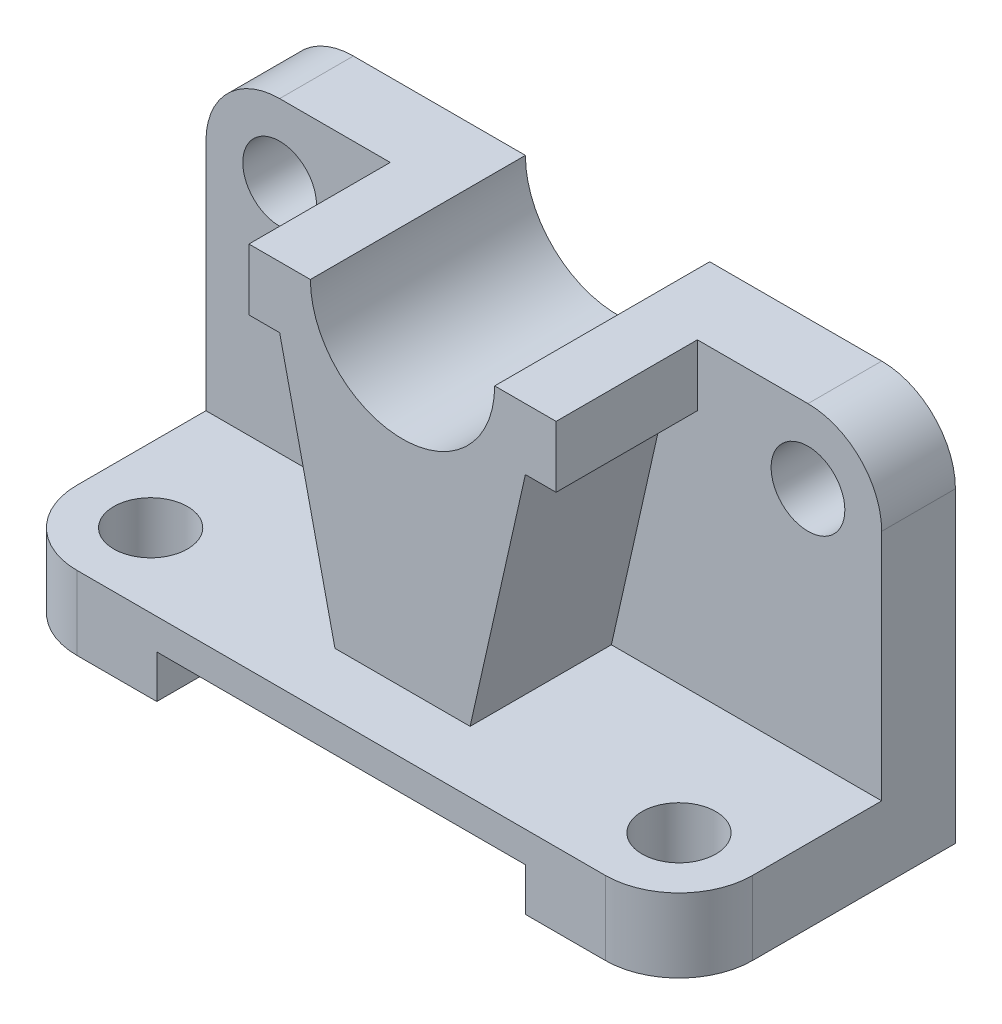
SolidWorks part; units mm, degrees
ref_plane "Front Plane" through (0, 0, 0) normal (0, 0, 1) x (1, 0, 0)
ref_plane "Top Plane" through (0, 0, 0) normal (0, 1, 0) x (1, 0, 0)
ref_plane "Right Plane" through (0, 0, 0) normal (1, 0, 0) x (0, 0, -1)
sketch "Sketch1" plane through (0, 0, 0) normal (1, 0, 0) x (0, 0, -1)
  line L0 (10.4243, 39.1655) -> (22.4243, 39.1655)
  line L1 (22.4243, 39.1655) -> (22.4243, -22.8345)
  line L2 (22.4243, -22.8345) -> (-22.5757, -22.8345)
  line L3 (-22.5757, -22.8345) -> (-22.5757, -10.8345)
  line L4 (-22.5757, -10.8345) -> (10.4243, -10.8345)
  line L5 (10.4243, 39.1655) -> (10.4243, -10.8345)
extrude "Boss-Extrude1" add sketch "Sketch1" along normal blind 110
fillet "Fillet1" radius 12 4 edges at (0, 39.1655, -16.4243) (0, -16.8345, 22.5757) (110, -16.8345, 22.5757) (110, 39.1655, -16.4243)
sketch "Sketch2" plane through (0, -10.8345, 0) normal (0, 1, 0) x (1, 0, 0)
  circle A0 centre (12, -10.5757) radius 6
  circle A1 centre (98, -10.5757) radius 6
extrude "Cut-Extrude1" cut sketch "Sketch2" against normal blind 12 contours A1 | A0
sketch "Sketch3" plane through (0, 0, -10.4243) normal (0, 0, 1) x (1, 0, 0)
  circle A0 centre (12, 27.1655) radius 6
  circle A1 centre (98, 27.1655) radius 6
extrude "Cut-Extrude3" cut sketch "Sketch3" against normal blind 12 contours A0 | A1
sketch "Sketch4" plane through (0, 0, 22.5757) normal (0, 0, 1) x (1, 0, 0)
  line L0 (25, -22.8345) -> (25, -15.8345)
  line L1 (98, -22.8345) -> (12, -22.8345) construction
  line L7 (25, -22.8345) -> (85, -22.8345)
  line L8 (25, -15.8345) -> (85, -15.8345)
  line L9 (85, -15.8345) -> (85, -22.8345)
extrude "Cut-Extrude4" cut sketch "Sketch4" against normal blind 60
sketch3d "3DSketch1"
  line L3 (30, 39.1655, -22.4243) -> (40, 39.1655, -22.4243)
  line L5 (70, 39.1655, -22.4243) -> (80, 39.1655, -22.4243)
  line L6 (30, 39.1655, -22.4243) -> (30, 29.1655, -22.4243)
  line L7 (30, 29.1655, -22.4243) -> (35, 29.1655, -22.4243)
  line L8 (80, 39.1655, -22.4243) -> (80, 29.1655, -22.4243)
  line L9 (80, 29.1655, -22.4243) -> (75, 29.1655, -22.4243)
  line L10 (35, 29.1655, -22.4243) -> (44, -10.8327, -22.4243)
  line L11 (55, -10.8327, -22.4243) -> (44, -10.8327, -22.4243) construction
  line L12 (44, -10.8327, -22.4243) -> (66, -10.8327, -22.4243)
  line L13 (75, 29.1655, -22.4243) -> (66, -10.8327, -22.4243)
  arc A0 (40, 39.1655, -22.4243) -> (70, 39.1655, -22.4243) centre (55, 39.1655, -22.4243) ccw
  point P5 (55, 39.1655, -7.4243)
  dimension "D1" = 12
extrude "Boss-Extrude2" add sketch "3DSketch1" along direction (0, 0, 1) on the side of the normal blind 35
sketch "Sketch5" plane through (0, 0, -10.4243) normal (0, 0, 1) x (1, 0, 0)
  line L0 (40, 39.1655) -> (70, 39.1655)
  arc A0 (70, 39.1655) -> (40, 39.1655) centre (55, 39.1655) cw
extrude "Cut-Extrude5" cut sketch "Sketch5" against normal blind 35
